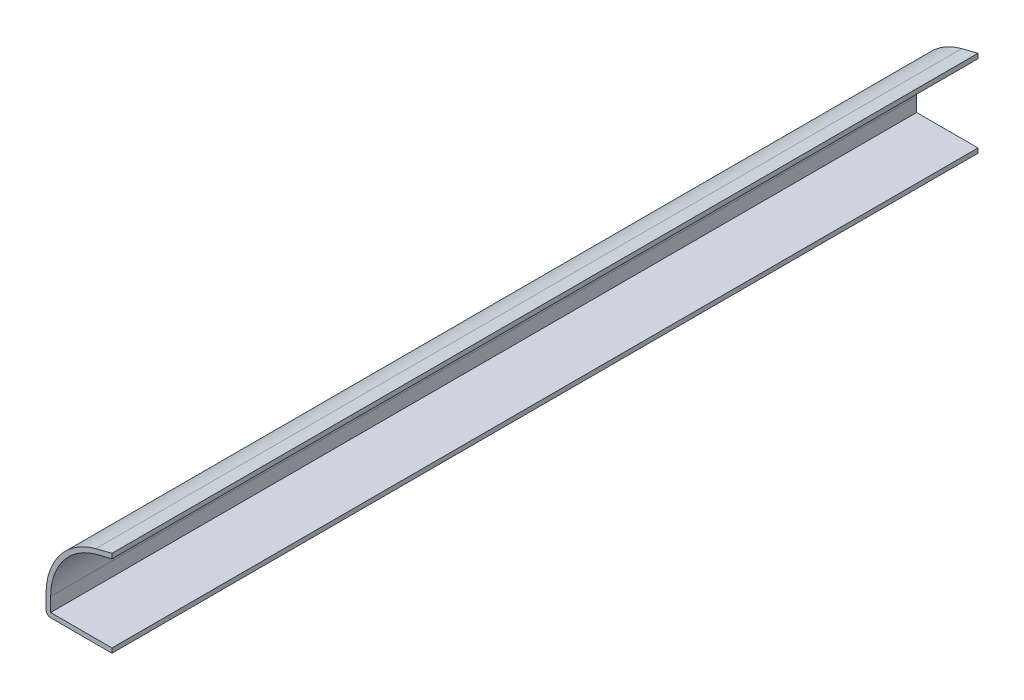
SolidWorks part; units mm, degrees
ref_plane "Front Plane" through (0, 0, 0) normal (0, 0, 1) x (1, 0, 0)
ref_plane "Top Plane" through (0, 0, 0) normal (0, 1, 0) x (1, 0, 0)
ref_plane "Right Plane" through (0, 0, 0) normal (1, 0, 0) x (0, 0, -1)
sketch "Sketch1" plane through (0, 0, 0) normal (0, 0, 1) x (1, 0, 0)
  line L0 (0, 0) -> (0, 16.6687) construction
  line L1 (0, 16.6687) -> (-3.1258, 15.875)
  line L2 (-12.7, 0) -> (0, 0)
  line L3 (-12.7, 0) -> (-12.7, 3.5657)
  arc A0 (-3.1258, 15.875) -> (-12.7, 3.5657) centre (0, 3.5657) ccw
  point P6 (0, 0)
  point P10 (-12.7, 2.5588)
  dimension "D1" = 12.7
  dimension "D2" = 16.6687
  dimension "D3" = 12.7
  dimension "D4" = 0.7937
extrude "Extrude-Thin1" add sketch "Sketch1" against normal blind 166.6875 thin thin type one direction reverse wall 0.889
fillet "Fillet1" radius 0.889 1 edges at (-12.7, 0, -83.3438)
sketch "Sketch2" plane through (0, 0, 0) normal (0, 0, 1) x (1, 0, 0)
  line L0 (0, 0.889) -> (0, 19.489)
extrude "Cut-Extrude1" cut sketch "Sketch2" against normal through all and the other way through all flip side to cut
